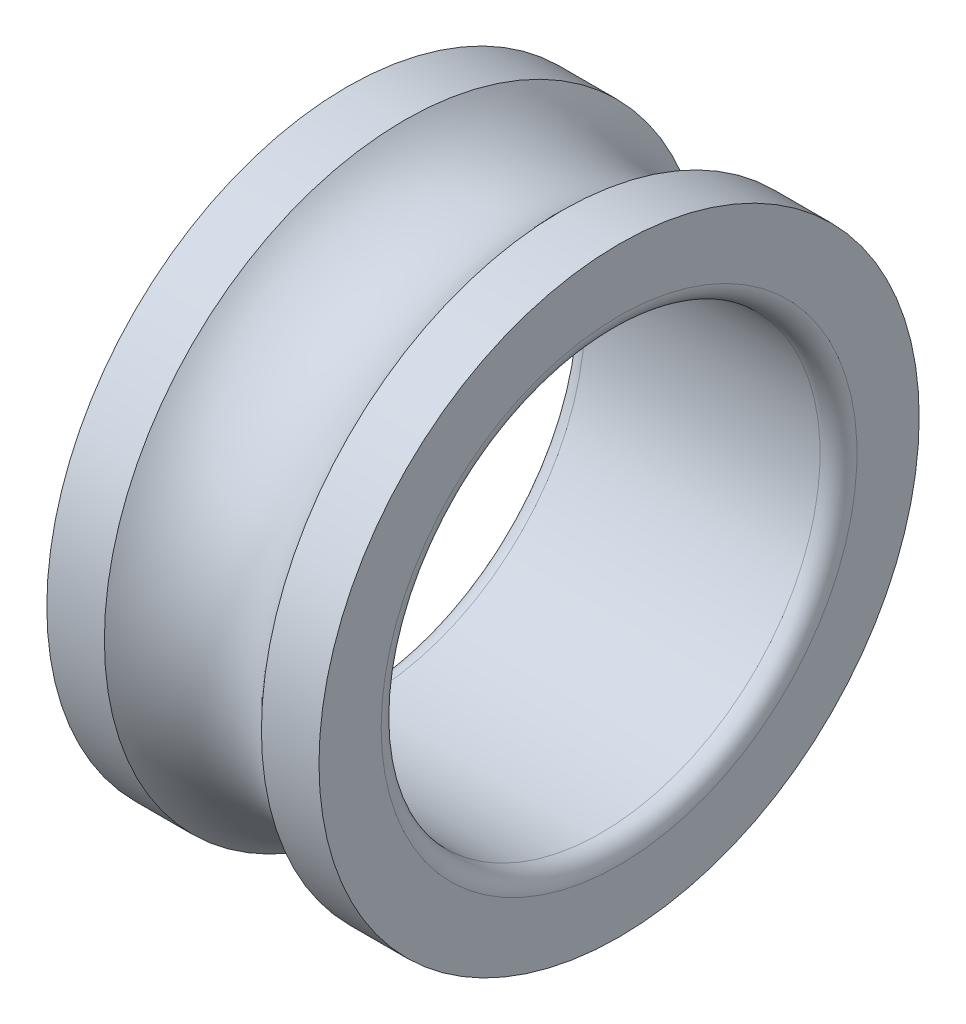
SolidWorks part; units mm, degrees
ref_plane "Front Plane" through (0, 0, 0) normal (0, 0, 1) x (1, 0, 0)
ref_plane "Top Plane" through (0, 0, 0) normal (0, 1, 0) x (1, 0, 0)
ref_plane "Right Plane" through (0, 0, 0) normal (1, 0, 0) x (0, 0, -1)
sketch "Sketch2" plane through (0, 0, 0) normal (0, 0, 1) x (1, 0, 0)
  line L0 (0, 0) -> (-14.2801, 0) construction
  line L1 (-14.2801, 0) -> (15.5, 0) construction
  line L2 (8.9443, 34.1852) -> (15.5, 34.1852)
  line L3 (-15.5, 34.1852) -> (-8.9443, 34.1852)
  line L4 (-15.5, 34.1852) -> (-15.5, 27.1)
  line L5 (-13.4, 25) -> (13.4, 25)
  line L6 (15.5, 34.1852) -> (15.5, 27.1)
  line L7 (-15.5, 34.1852) -> (15.5, 25) construction
  line L8 (-15.5, 25) -> (15.5, 34.1852) construction
  arc A0 (-8.9443, 34.1852) -> (8.9443, 34.1852) centre (0, 42.1852) ccw
  arc A1 (13.4, 25) -> (15.5, 27.1) centre (13.4, 27.1) ccw
  arc A2 (-15.5, 27.1) -> (-13.4, 25) centre (-13.4, 27.1) ccw
  point P3 (0, 29.5926)
  dimension "D5" = 12
  dimension "D6" = 2.1
  dimension "D1" = 31
  dimension "D2" = 25
  dimension "D3" = 34.1852
  dimension "D4" = 8
revolve "Revolve1" add sketch "Sketch2" angle 360 about L1
